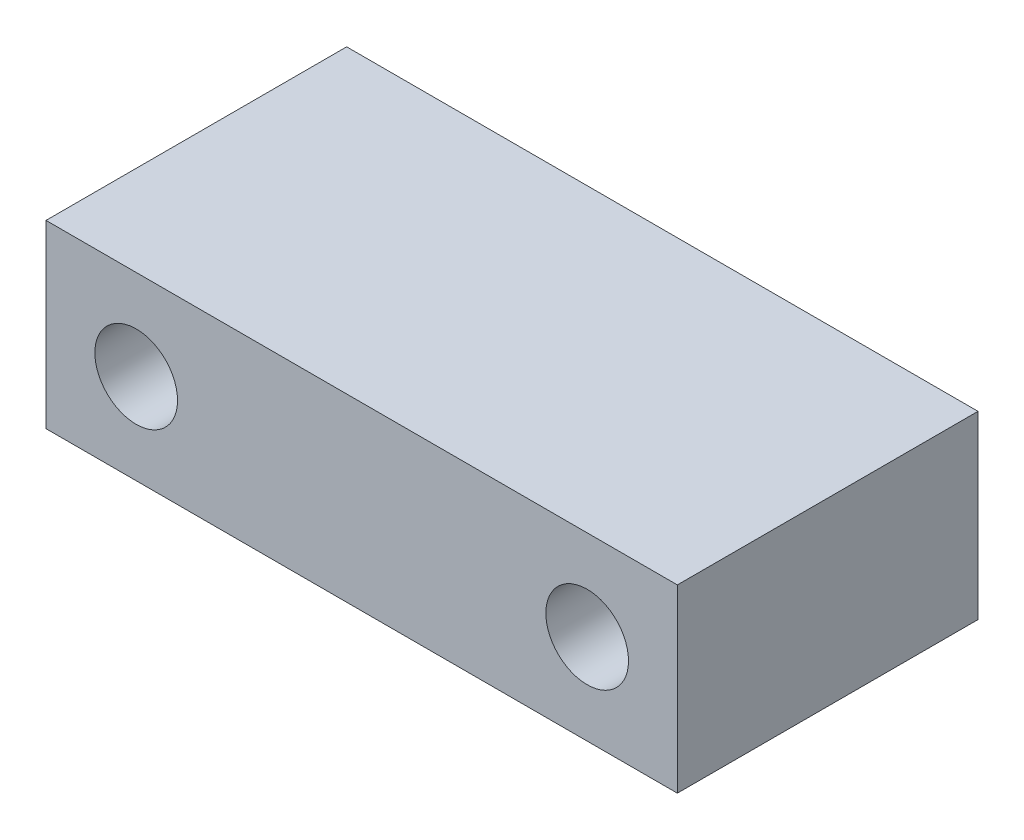
SolidWorks part; units mm, degrees
ref_plane "Front" through (0, 0, 0) normal (0, 0, 1) x (1, 0, 0)
ref_plane "Top" through (0, 0, 0) normal (0, 1, 0) x (1, 0, 0)
ref_plane "Right" through (0, 0, 0) normal (1, 0, 0) x (0, 0, -1)
sketch "草图1" plane through (0, 0, 0) normal (0, 0, 1) x (1, 0, 0)
  line L1 (-21, -6) -> (21, -6)
  line L2 (-21, -6) -> (-21, 6)
  line L3 (-21, 6) -> (21, 6)
  line L4 (21, -6) -> (21, 6)
  line L5 (-21, -6) -> (21, 6) construction
  line L6 (-21, 6) -> (21, -6) construction
  point P0 (0, 0)
  dimension "D1" = 42
  dimension "D2" = 12
extrude "凸台-拉伸1" add sketch "草图1" along normal blind 20
sketch "草图2" plane through (0, 0, 20) normal (0, 0, 1) x (1, 0, 0)
  line L1 (-21, 6) -> (-21, -6) construction
  line L2 (21, -6) -> (21, 6) construction
  line L3 (21, 6) -> (-21, 6) construction
  point P0 (-15, 0)
  point P1 (15, 0)
  dimension "D1" = 6
  dimension "D2" = 6
  dimension "D3" = 6
  dimension "D4" = 6
hole_wizard "Ø5.5 (5.5) 直径孔1" positions "草图3" profile "草图4" hole size "Ø5.5" standard "GB" end condition up to next
sketch "草图3" plane through (0, 0, 20) normal (0, 0, 1) x (1, 0, 0)
  point P0 (-15, 0)
  point P3 (15, 0)
sketch "草图4" plane through (-15, 0, 20) normal (1, 0, 0) x (0, -1, 0)
  line L0 (0, 0) -> (0, 20)
  line L1 (0, 20) -> (2.75, 20)
  line L2 (2.75, 20) -> (2.75, 0)
  line L5 (2.75, 0) -> (0, 0)
  line L11 (0, -6.35) -> (0, 107.95) construction
  dimension "通孔孔直径" = 5.5
  dimension "通孔孔深度" = 20
